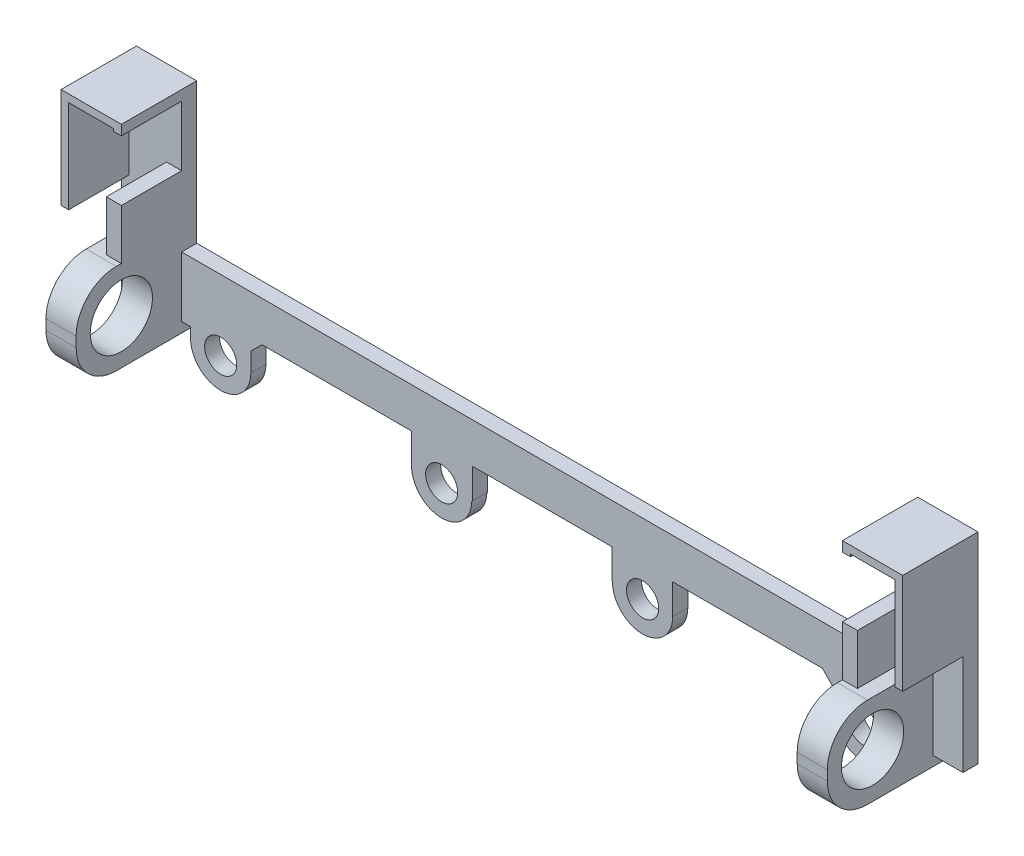
SolidWorks part; units mm, degrees
ref_plane "Front" through (0, 0, 0) normal (0, 0, 1) x (1, 0, 0)
ref_plane "Top" through (0, 0, 0) normal (0, 1, 0) x (1, 0, 0)
ref_plane "Right" through (0, 0, 0) normal (1, 0, 0) x (0, 0, -1)
sketch "Sketch1" plane through (0, 0, 0) normal (0, 0, 1) x (1, 0, 0)
  line L0 (-35.8888, 0) -> (35.8888, 0)
  line L2 (35.8888, -4) -> (13, -4)
  line L5 (6.9472, -7) -> (7, -7)
  line L6 (6.9472, -7) -> (6.9472, -4)
  line L7 (13, -7) -> (13, -4)
  line L8 (6.9472, -4) -> (-6.9472, -4)
  line L9 (35.8888, 0) -> (35.8888, 14)
  line L10 (35.8888, 14) -> (40.8888, 14)
  line L11 (40.8888, 14) -> (40.8888, -4)
  line L12 (40.8888, -4) -> (35.8888, -4)
  line L13 (-40.8888, -4) -> (-35.8888, -4)
  line L14 (-40.8888, 14) -> (-40.8888, -4)
  line L15 (-35.8888, 14) -> (-40.8888, 14)
  line L16 (-35.8888, 0) -> (-35.8888, 14)
  line L17 (-13, -7) -> (-13, -4)
  line L18 (-6.9472, -7) -> (-6.9472, -4)
  line L19 (-6.9472, -7) -> (-7, -7)
  line L20 (-35.8888, -4) -> (-13, -4)
  arc A0 (7, -7) -> (13, -7) centre (10, -7) ccw
  circle A1 centre (10, -7) radius 1.6
  circle A2 centre (-10, -7) radius 1.6
  arc A3 (-7, -7) -> (-13, -7) centre (-10, -7) cw
extrude "Boss-Extrude1" add sketch "Sketch1" along normal blind 1.5
sketch "Sketch2" plane through (0, 0, 1.5) normal (0, 0, 1) x (1, 0, 0)
  line L0 (40.8888, 14) -> (41.8888, 14)
  line L1 (40.8888, 14) -> (40.8888, -4)
  line L2 (40.8888, -4) -> (41.8888, -4)
  line L3 (41.8888, -4) -> (41.8888, 14)
  line L5 (-41.8888, -4) -> (-41.8888, 14)
  line L6 (-40.8888, -4) -> (-41.8888, -4)
  line L7 (-40.8888, 14) -> (-40.8888, -4)
  line L8 (-40.8888, 14) -> (-41.8888, 14)
extrude "Boss-Extrude2" add sketch "Sketch2" against normal up to surface (1.5 mm away) up to face at (0, -0.8889, 0)
sketch "Sketch3" plane through (0, 0, 1.5) normal (0, 0, 1) x (1, 0, 0)
  line L0 (35.8888, 14) -> (41.8888, 14)
  line L1 (41.8888, 14) -> (41.8888, 4)
  line L2 (41.8888, -4) -> (41.8888, 14) construction
  line L3 (35.8888, 14) -> (35.8888, 13)
  line L4 (35.8888, 14) -> (35.8888, 0) construction
  line L5 (41.8888, 4) -> (41.3888, 4)
  line L6 (41.3888, 4) -> (41.3888, 13.5)
  line L7 (35.8888, 13) -> (36.6888, 13)
  line L8 (36.6888, 13) -> (36.6888, 13.5)
  line L9 (36.6888, 13.5) -> (41.3888, 13.5)
  line L11 (-36.6888, 13.5) -> (-41.3888, 13.5)
  line L12 (-36.6888, 13) -> (-36.6888, 13.5)
  line L13 (-35.8888, 13) -> (-36.6888, 13)
  line L14 (-41.3888, 4) -> (-41.3888, 13.5)
  line L15 (-41.8888, 4) -> (-41.3888, 4)
  line L16 (-35.8888, 14) -> (-35.8888, 13)
  line L17 (-41.8888, 14) -> (-41.8888, 4)
  line L18 (-35.8888, 14) -> (-41.8888, 14)
extrude "Boss-Extrude3" add sketch "Sketch3" along normal blind 6 contours L11 L14 L15 L17 L18 L16 L13 L12 | L9 L6 L5 L1 L0 L3 L7 L8
sketch "Sketch4" plane through (0, 0, 7.5) normal (0, 0, 1) x (1, 0, 0)
  line L0 (-41.3888, 4) -> (-41.1388, 4)
  line L1 (-41.1388, 4) -> (-41.1388, 13.1289)
  line L2 (-36.6888, 13.5) -> (-36.6888, 13.25)
  line L3 (-36.6888, 13) -> (-36.6888, 13.5) construction
  line L4 (-36.6888, 13.25) -> (-41.1388, 13.25)
  line L5 (-41.1388, 13.25) -> (-41.1388, 13.1289)
  line L6 (-36.6888, 13.5) -> (-41.3888, 13.5)
  line L7 (-41.3888, 13.5) -> (-41.3888, 4)
  line L9 (41.3888, 13.5) -> (41.3888, 4)
  line L10 (36.6888, 13.5) -> (41.3888, 13.5)
  line L11 (41.1388, 13.25) -> (41.1388, 13.1289)
  line L12 (36.6888, 13.25) -> (41.1388, 13.25)
  line L13 (36.6888, 13.5) -> (36.6888, 13.25)
  line L14 (41.1388, 4) -> (41.1388, 13.1289)
  line L15 (41.3888, 4) -> (41.1388, 4)
extrude "Boss-Extrude4" add sketch "Sketch4" against normal up to surface (6 mm away) up to face at (0, 1.9231, 1.5)
sketch "Sketch5" plane through (0, 0, 1.5) normal (0, 0, 1) x (1, 0, 0)
  line L1 (-35.8888, 0) -> (-35.8888, 13) construction
  line L2 (-35.8888, 7) -> (-37.3888, 7)
  line L3 (-37.3888, 7) -> (-37.3888, 0)
  line L4 (-37.3888, 0) -> (-35.8888, 0)
  line L5 (-35.8888, 0) -> (-35.8888, 7)
  line L6 (35.8888, 0) -> (35.8888, 7)
  line L7 (37.3888, 0) -> (35.8888, 0)
  line L8 (37.3888, 7) -> (37.3888, 0)
  line L9 (35.8888, 7) -> (37.3888, 7)
extrude "Boss-Extrude5" add sketch "Sketch5" along normal blind 6
sketch "Sketch6" plane through (0, 0, 1.5) normal (0, 0, 1) x (1, 0, 0)
  line L0 (41.8888, -4) -> (41.8888, -6)
  line L1 (41.8888, -6) -> (29.8888, -6)
  line L2 (29.8888, -6) -> (27.8888, -4)
  line L3 (13, -4) -> (41.8888, -4) construction
  line L4 (27.8888, -4) -> (41.8888, -4)
  line L6 (-27.8888, -4) -> (-41.8888, -4)
  line L7 (-29.8888, -6) -> (-27.8888, -4)
  line L8 (-41.8888, -6) -> (-29.8888, -6)
  line L9 (-41.8888, -4) -> (-41.8888, -6)
extrude "Boss-Extrude6" add sketch "Sketch6" against normal up to surface (1.5 mm away) up to face at (0, -0.8889, 0)
sketch "Sketch7" plane through (0, 0, 1.5) normal (0, 0, 1) x (1, 0, 0)
  line L0 (35.8888, 0) -> (35.8888, -6)
  line L1 (29.8888, -6) -> (41.8888, -6) construction
  line L2 (35.8888, -6) -> (38.8888, -6)
  line L3 (38.8888, -6) -> (38.8888, 0)
  line L4 (38.8888, 0) -> (35.8888, 0)
  line L6 (-38.8888, 0) -> (-35.8888, 0)
  line L7 (-38.8888, -6) -> (-38.8888, 0)
  line L8 (-35.8888, -6) -> (-38.8888, -6)
  line L9 (-35.8888, 0) -> (-35.8888, -6)
extrude "Boss-Extrude7" add sketch "Sketch7" along normal blind 12
sketch "Sketch8" plane through (0, 0, 13.5) normal (0, 0, 1) x (1, 0, 0)
  line L0 (-35.8888, 0) -> (-35.8888, -9)
  line L1 (-35.8888, -9) -> (-38.8888, -9)
  line L2 (-38.8888, -9) -> (-38.8888, 0)
  line L3 (-38.8888, 0) -> (-35.8888, 0)
  line L5 (38.8888, 0) -> (35.8888, 0)
  line L6 (38.8888, -9) -> (38.8888, 0)
  line L7 (35.8888, -9) -> (38.8888, -9)
  line L8 (35.8888, 0) -> (35.8888, -9)
extrude "Boss-Extrude8" add sketch "Sketch8" against normal up to surface (13.5 mm away) up to face at (0, -1.8182, 0)
sketch "Sketch10" plane through (0, 0, 13.5) normal (0, 0, 1) x (1, 0, 0)
  line L0 (-35.8888, -9) -> (-35.8888, -7)
  line L1 (-35.8888, -9) -> (-35.8888, 0) construction
  line L2 (-35.8888, -7) -> (-38.8888, -7)
  line L3 (-38.8888, 0) -> (-38.8888, -9) construction
  line L4 (-38.8888, -7) -> (-38.8888, -9)
  line L5 (-38.8888, -9) -> (-35.8888, -9)
  line L6 (38.8888, -9) -> (38.8888, -7)
  line L7 (38.8888, -9) -> (38.8888, 0) construction
  line L8 (38.8888, -7) -> (35.8888, -7)
  line L9 (35.8888, 0) -> (35.8888, -9) construction
  line L10 (35.8888, -7) -> (35.8888, -9)
  line L11 (35.8888, -9) -> (38.8888, -9)
extrude "Cut-Extrude2" cut sketch "Sketch10" against normal blind 141
sketch "Sketch11" plane through (0, 0, 13.5) normal (0, 0, 1) x (1, 0, 0)
  line L0 (-35.8888, 0) -> (-35.8888, 2)
  line L1 (-35.8888, 0) -> (-35.8888, 7) construction
  line L2 (-35.8888, 0) -> (-38.8888, 0)
  line L3 (-38.8888, 0) -> (-38.8888, 2)
  line L4 (-38.8888, 2) -> (-35.8888, 2)
  line L5 (38.8888, 0) -> (38.8888, 2)
  line L6 (38.8888, 2) -> (35.8888, 2)
  line L7 (35.8888, 7) -> (35.8888, 0) construction
  line L8 (35.8888, 2) -> (35.8888, 0)
  line L9 (35.8888, 0) -> (38.8888, 0)
extrude "Boss-Extrude9" add sketch "Sketch11" against normal up to surface (12 mm away) up to face at (11.6, -7, 1.5)
sketch "Sketch12" plane through (38.8888, 0, 0) normal (1, 0, 0) x (0, 0, -1)
  line L3 (-13.5, 2) -> (-12, 2)
  line L4 (-1.5, 2) -> (-13.5, 2) construction
  line L5 (-12, 2) -> (-12, -7)
  line L6 (0, -7) -> (-13.5, -7) construction
  line L7 (-12, -7) -> (-13.5, -7)
  line L8 (-13.5, -7) -> (-13.5, 2)
  circle A0 centre (-7.5, -2.5) radius 3.1
extrude "Cut-Extrude6" cut sketch "Sketch12" against normal blind 86
fillet "Fillet4" radius 4 4 edges at (37.3888, -7, 12) (37.3888, 2, 12) (-37.3888, -7, 12) (-37.3888, 2, 12)
sketch "Sketch13" plane through (0, 0, 1.5) normal (0, 0, 1) x (1, 0, 0)
  line L1 (-29, -7) -> (-29, -2.5963)
  line L2 (-35, -7) -> (-35, -2.5963)
  line L3 (-35, -2.5963) -> (-29, -2.5963)
  line L4 (35, -2.5963) -> (29, -2.5963)
  line L5 (35, -7) -> (35, -2.5963)
  line L6 (29, -7) -> (29, -2.5963)
  arc A0 (-35, -7) -> (-29, -7) centre (-32, -7) ccw
  circle A1 centre (-32, -7) radius 1.6
  circle A2 centre (32, -7) radius 1.6
  arc A3 (35, -7) -> (29, -7) centre (32, -7) cw
extrude "Boss-Extrude10" add sketch "Sketch13" against normal up to surface (1.5 mm away) up to face at (0, -3.0667, 0)
sketch "Sketch14" plane through (0, 0, 1.5) normal (0, 0, 1) x (1, 0, 0)
  circle A0 centre (-32, -7) radius 1.6
  circle A1 centre (32, -7) radius 1.6
extrude "Cut-Extrude7" cut sketch "Sketch14" against normal blind 1.5
